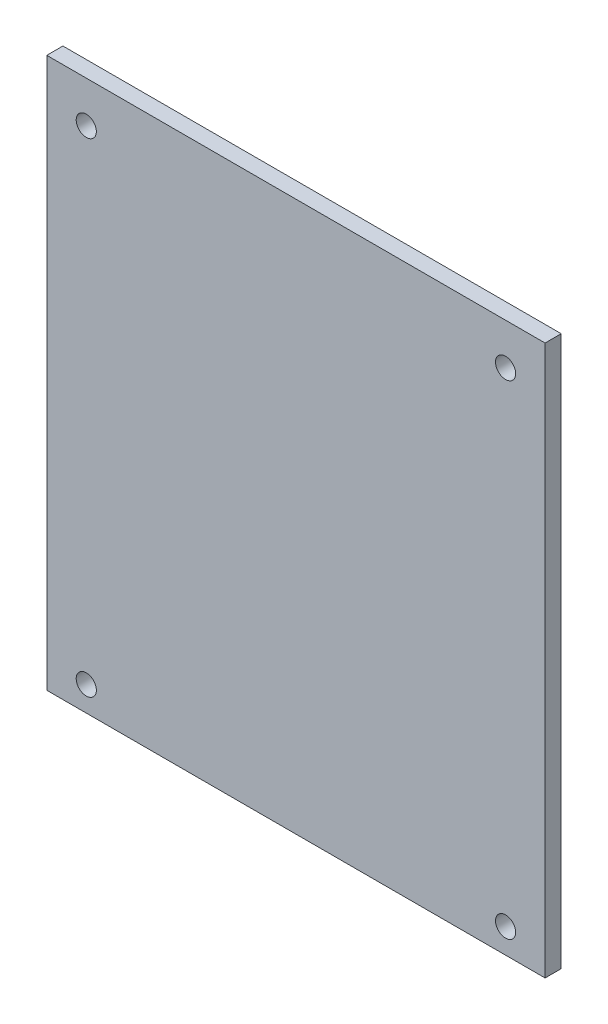
SolidWorks part; units mm, degrees
ref_plane "Front Plane" through (0, 0, 0) normal (0, 0, 1) x (1, 0, 0)
ref_plane "Top Plane" through (0, 0, 0) normal (0, 1, 0) x (1, 0, 0)
ref_plane "Right Plane" through (0, 0, 0) normal (1, 0, 0) x (0, 0, -1)
sketch "Sketch1" plane through (0, 0, 0) normal (0, 0, 1) x (1, 0, 0)
  line L1 (0, 86.614) -> (78.486, 86.614)
  line L2 (0, 86.614) -> (0, 0)
  line L3 (0, 0) -> (78.486, 0)
  line L4 (78.486, 86.614) -> (78.486, 0)
  dimension "D4" = 78.486
  dimension "D5" = 86.614
extrude "Boss-Extrude1" add sketch "Sketch1" along normal blind 2.54
sketch "Sketch2" plane through (0, 0, 2.54) normal (0, 0, 1) x (1, 0, 0)
  line L0 (6.223, 80.1116) -> (72.263, 80.1116) construction
  line L5 (72.263, 80.1116) -> (72.263, 3.9116) construction
  line L6 (72.263, 3.9116) -> (6.223, 3.9116) construction
  line L7 (6.223, 3.9116) -> (6.223, 80.1116) construction
  line L8 (39.243, 86.614) -> (39.243, 0) construction
  line L9 (6.223, 42.0116) -> (72.263, 42.0116) construction
  line L10 (0, 0) -> (78.486, 0) construction
  line L11 (78.486, 86.614) -> (0, 86.614) construction
  circle A0 centre (6.223, 80.1116) radius 1.5875
  circle A1 centre (72.263, 80.1116) radius 1.5875
  circle A2 centre (72.263, 3.9116) radius 1.5875
  circle A3 centre (6.223, 3.9116) radius 1.5875
  point P18 (39.243, 42.0116)
  point P22 (39.243, 43.307)
  dimension "D3" = 3.175
  dimension "D1" = 76.2
  dimension "D2" = 66.04
  dimension "D4" = 1.2954
extrude "Cut-Extrude1" cut sketch "Sketch2" against normal up to surface (2.54 mm away) up to face at (39.243, 43.307, 0)
